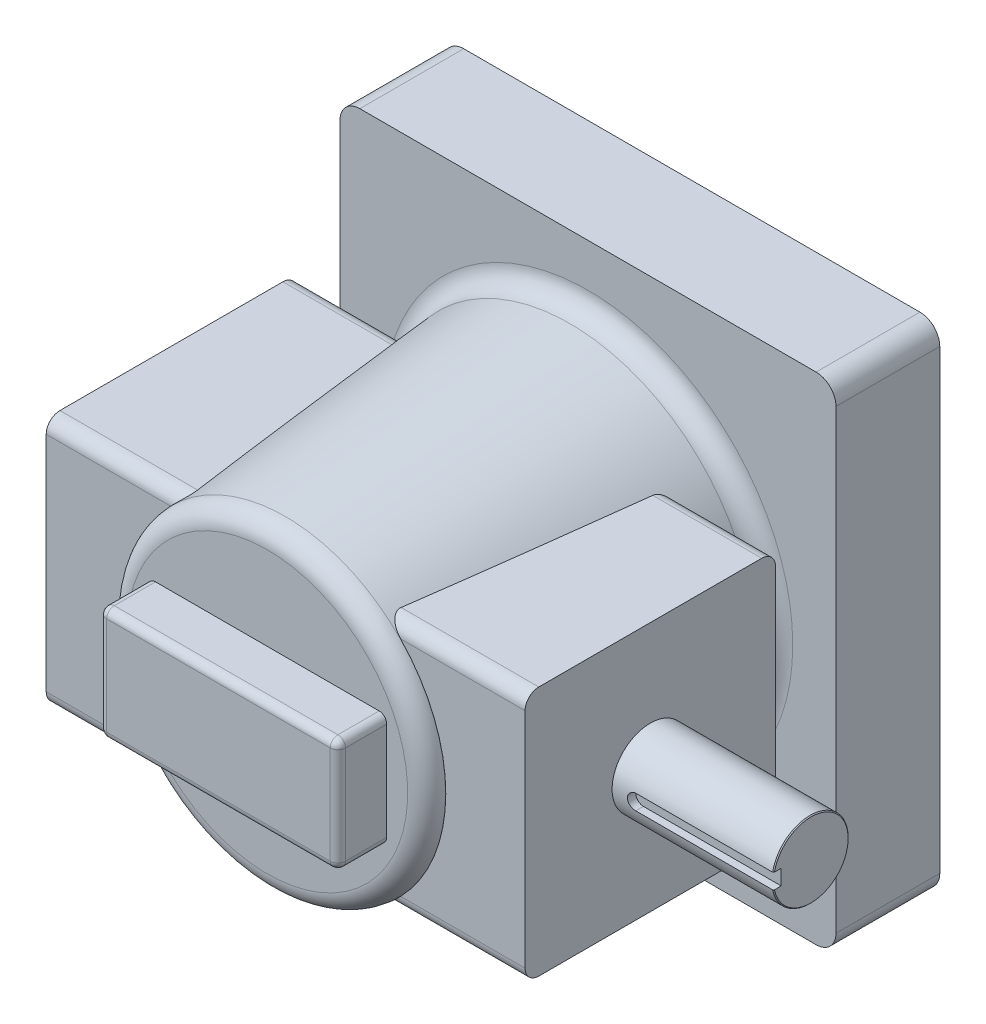
SolidWorks part; units mm, degrees
ref_plane "Front Plane" through (0, 0, 0) normal (0, 0, 1) x (1, 0, 0)
ref_plane "Top Plane" through (0, 0, 0) normal (0, 1, 0) x (1, 0, 0)
ref_plane "Right Plane" through (0, 0, 0) normal (1, 0, 0) x (0, 0, -1)
ref_plane "D" through (0, 0, 116.84) normal (0, 0, 1) x (1, 0, 0)
ref_plane "G" through (0, 0, 196.85) normal (0, 0, 1) x (1, 0, 0)
sketch "Sketch1" plane through (0, 0, 0) normal (0, 0, 1) x (1, 0, 0)
  line L0 (-103.124, -103.124) -> (103.124, 103.124) construction
  line L1 (-103.124, 103.124) -> (103.124, 103.124)
  line L2 (-103.124, 103.124) -> (-103.124, -103.124)
  line L3 (-103.124, -103.124) -> (103.124, -103.124)
  line L4 (103.124, 103.124) -> (103.124, -103.124)
  dimension "D1" = 206.248
extrude "C dim" add sketch "Sketch1" along normal blind 43.18
ref_plane "F" through (166.37, 0, 0) normal (1, 0, 0) x (0, 0, -1)
sketch "A" plane through (0, 0, 0) normal (1, 0, 0) x (0, 0, -1)
  line L0 (-116.84, 47.2186) -> (-116.84, -47.2186) construction
  line L1 (-116.84, 0) -> (0, 0) construction
  circle A0 centre (-116.84, 0) radius 15.875
  dimension "D1" = 31.75
extrude "Shaft" add sketch "A" along normal up to surface (153.67 mm away) from offset 12.7 separate body up to plane "F"
ref_plane "E" through (99.568, 0, 0) normal (1, 0, 0) x (0, 0, -1)
sketch "Sketch3" plane through (0, 0, 0) normal (1, 0, 0) x (0, 0, -1)
  line L0 (-64.77, -52.07) -> (-168.91, 52.07) construction
  line L1 (-64.77, 52.07) -> (-168.91, 52.07)
  line L2 (-64.77, 52.07) -> (-64.77, -52.07)
  line L3 (-64.77, -52.07) -> (-168.91, -52.07)
  line L4 (-168.91, 52.07) -> (-168.91, -52.07)
  line L6 (0, 103.124) -> (-43.18, 103.124) construction
  line L7 (-43.18, 103.124) -> (-21.59, 103.124) construction
  line L8 (-64.77, 52.07) -> (-43.18, 52.07) construction
  line L9 (-43.18, 103.124) -> (-43.18, -103.124) construction
  point P4 (-116.84, 0)
extrude "Boss-Extrude3" add sketch "Sketch3" along normal up to surface (99.568 mm away) separate body up to plane "E"
mirror "Mirror2" about plane through (0, 0, 0) normal (1, 0, 0) of bodies 103
fillet "Fillet1" radius 5.715 4 edges at (49.784, -52.07, 64.77) (49.784, -52.07, 168.91) (49.784, 52.07, 64.77) (49.784, 52.07, 168.91)
fillet "Fillet4" radius 5.715 4 edges at (-49.784, -52.07, 64.77) (-49.784, -52.07, 168.91) (-49.784, 52.07, 64.77) (-49.784, 52.07, 168.91)
sketch "Sketch4" plane through (0, 0, 43.18) normal (0, 0, 1) x (1, 0, 0)
  line L0 (0, 52.07) -> (0, 103.124) construction
  line L1 (0, 52.07) -> (0, -52.07) construction
  line L3 (103.124, 103.124) -> (-103.124, 103.124) construction
  line L4 (-99.568, 52.07) -> (99.568, 52.07) construction
  circle A0 centre (0, 0) radius 77.597
  point P7 (0, 77.597)
extrude "Boss-Extrude4" add sketch "Sketch4" along normal offset from surface 7.62 draft 5
fillet "Fillet2" radius 8.255 6 edges at (-65.9304, 0, 176.53) (103.124, -103.124, 21.59) (-103.124, -103.124, 21.59) (-103.124, 103.124, 21.59) (103.124, 103.124, 21.59) (77.597, 0, 43.18)
sketch "Sketch5" plane through (0, 0, 176.53) normal (0, 0, 1) x (1, 0, 0)
  line L0 (0, 0) -> (52.2042, 0) construction
  line L1 (-52.2042, 26.1021) -> (52.2042, 26.1021) construction
  line L2 (-52.2042, 26.1021) -> (-52.2042, -26.1021) construction
  line L3 (-52.2042, -26.1021) -> (52.2042, -26.1021) construction
  line L4 (52.2042, 26.1021) -> (52.2042, -26.1021) construction
  line L5 (-49.6642, 23.5621) -> (49.6642, 23.5621)
  line L6 (49.6642, 23.5621) -> (49.6642, -23.5621)
  line L7 (-49.6642, -23.5621) -> (49.6642, -23.5621)
  line L8 (-49.6642, 23.5621) -> (-49.6642, -23.5621)
  circle A0 centre (0, 0) radius 58.3661 construction
  dimension "D1" = 2.54
extrude "Boss-Extrude5" add sketch "Sketch5" along normal up to surface (20.32 mm away) up to plane "G"
chamfer "Chamfer1" distance 0.381 angle 45 1 edges at (166.37, 0, 100.965)
fillet "Fillet3" radius 3.175 8 edges at (0, -23.5621, 196.85) (49.6642, 0, 196.85) (0, 23.5621, 196.85) (-49.6642, 0, 196.85) (-49.6642, -23.5621, 186.69) (49.6642, -23.5621, 186.69) (-49.6642, 23.5621, 186.69) (49.6642, 23.5621, 186.69)
sketch "Sketch6" plane through (0, 0, 116.84) normal (0, 0, 1) x (1, 0, 0)
  line L0 (166.37, 0) -> (109.093, 0) construction
  line L1 (166.37, -15.494) -> (166.37, 15.494) construction
  line L2 (166.37, -3.175) -> (109.093, -3.175)
  line L3 (166.37, 3.175) -> (109.093, 3.175)
  line L4 (105.918, 0) -> (99.568, 0) construction
  line L6 (109.093, 3.175) -> (109.093, -3.175) construction
  line L7 (99.568, 46.355) -> (99.568, -46.355) construction
  arc A0 (166.37, -3.175) -> (166.37, 3.175) centre (166.37, 0) ccw
  arc A1 (109.093, 3.175) -> (109.093, -3.175) centre (109.093, 0) ccw
  point P5 (137.7315, 0)
  dimension "D1" = 6.35
extrude "B" cut sketch "Sketch6" along normal through all from offset 12.3698
mirror "Mirror6" [suppressed] about plane through (0, 0, 0) normal (1, 0, 0)
combine bodies "Combine1" operation type add bodies to combine 107 108
